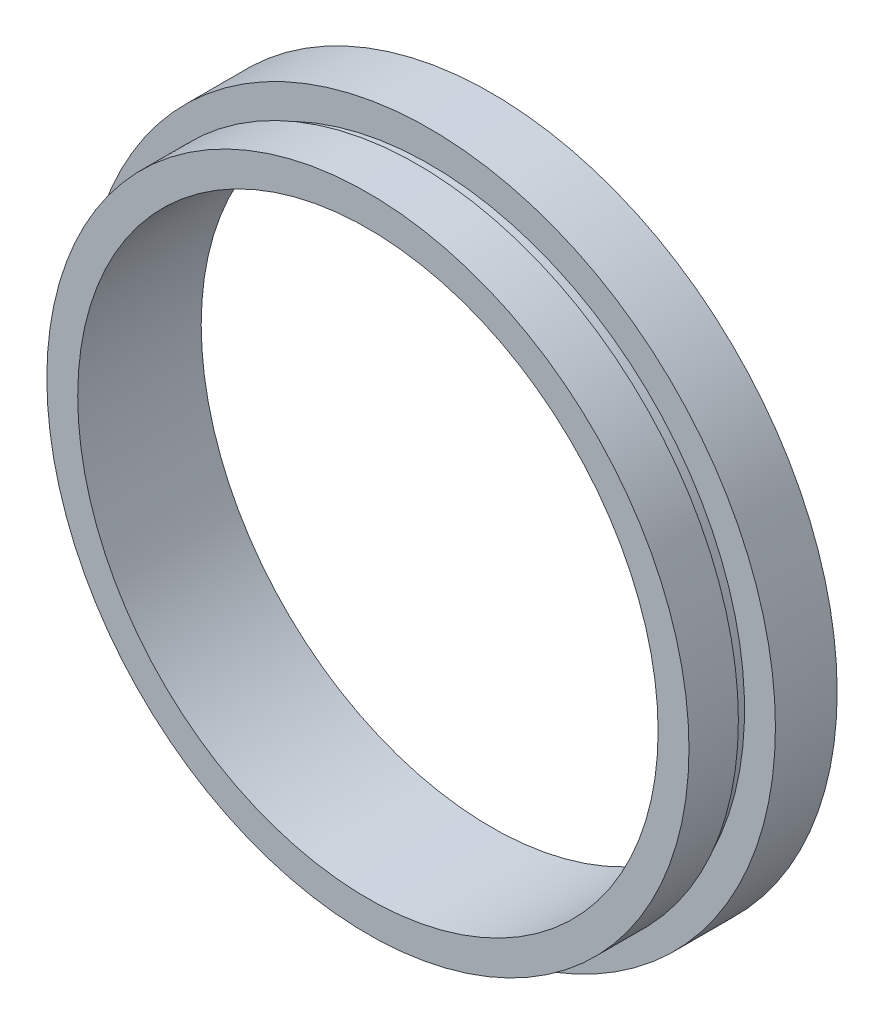
SolidWorks part; units mm, degrees
ref_plane "前视基准面" through (0, 0, 0) normal (0, 0, 1) x (1, 0, 0)
ref_plane "上视基准面" through (0, 0, 0) normal (0, 1, 0) x (1, 0, 0)
ref_plane "右视基准面" through (0, 0, 0) normal (1, 0, 0) x (0, 0, -1)
sketch "草图1" plane through (0, 0, 0) normal (0, 1, 0) x (1, 0, 0)
  line L0 (0, 19.1406) -> (0, -28.4043) construction
  line L1 (23.5, 0) -> (23.5, 10)
  line L2 (23.5, 0) -> (26, 0)
  line L3 (26, 0) -> (26, 4)
  line L4 (26, 4) -> (25.5, 4)
  line L5 (25.5, 4) -> (25.5, 5)
  line L6 (25.5, 5) -> (28, 5)
  line L7 (28, 5) -> (28, 10)
  line L8 (28, 10) -> (23.5, 10)
  dimension "D3" = 25.5
  dimension "D1" = 23.5
  dimension "D2" = 26
  dimension "D4" = 28
  dimension "D5" = 1
  dimension "D6" = 5
  dimension "D7" = 10
revolve "旋转1" add sketch "草图1" angle 360 about L0
cosmetic thread "装饰螺纹线1" parameters "D1"=5, "D2"=48
cosmetic thread "装饰螺纹线2" parameters "D1"=4, "D2"=51
